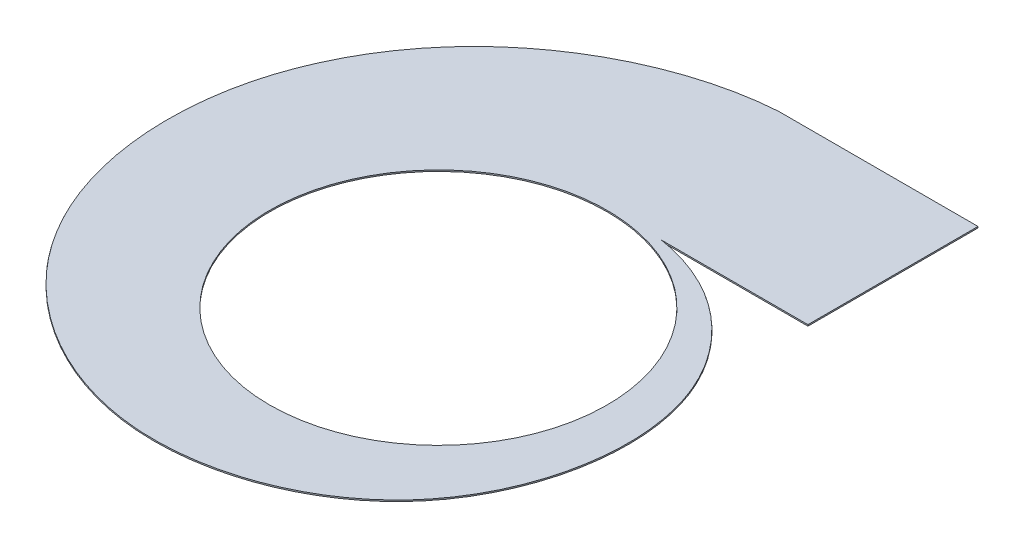
SolidWorks part; units mm, degrees
ref_plane "Front Plane" through (0, 0, 0) normal (0, 0, 1) x (1, 0, 0)
ref_plane "Top Plane" through (0, 0, 0) normal (0, 1, 0) x (1, 0, 0)
ref_plane "Right Plane" through (0, 0, 0) normal (1, 0, 0) x (0, 0, -1)
sketch "Sketch2" plane through (0, 0, 0) normal (0, 1, 0) x (1, 0, 0)
  circle A0 centre (0, 0) radius 250
  dimension "D1" = 500
curve "Helix/Spiral1"
sketch "Sketch4" plane through (0, 0, 0) normal (1, 0, 0) x (0, 0, -1)
  line L1 (250, 0) -> (248, 0)
  line L2 (250, 0) -> (250, 200)
  line L3 (250, 200) -> (248, 200)
  line L4 (248, 0) -> (248, 200)
  dimension "D1" = 250
  dimension "D2" = 2
  dimension "D3" = 200
sweep "Sweep1" add profiles "Sketch4" path "Helix/Spiral1"
sketch3d "3DSketch1"
  line L0 (0, 0, 0) -> (0, 273.3614, 0) construction
sketch "Sketch5" plane through (0, 0, 0) normal (0, -1, 0) x (1, 0, 0)
  line L0 (0, -250) -> (0, -500)
  spline S0 degree 3 poles (0, -250) (8.1812, -251.3021) (16.4905, -252.2022) (33.2838, -253.165) (41.7679, -253.2276) (58.8255, -252.4898) (67.399, -251.6894) (84.5468, -249.209) (93.1211, -247.529) (110.1794, -243.282) (118.6635, -240.7149) (135.4488, -234.6958) (143.7502, -231.2437) (160.0773, -223.4662) (168.1031, -219.1409) (183.7869, -209.6384) (191.4449, -204.4612) (206.3026, -193.2864) (213.5023, -187.2887) (227.3553, -174.5137) (234.0086, -167.7364) (246.6848, -153.4526) (252.7076, -145.946) (264.0432, -130.263) (269.3559, -122.0865) (279.1976, -105.1317) (283.7264, -96.3534) (291.933, -78.271) (295.6107, -68.9668) (302.0553, -49.9163) (304.8221, -40.1699) (309.3934, -20.325) (311.1979, -10.2265) (313.8021, 10.2265) (314.6018, 20.5811) (315.1636, 41.4454) (314.9257, 51.9551) (313.3899, 73.0247) (312.0919, 83.5846) (308.4241, 104.6469) (306.0542, 115.1492) (300.2417, 135.9868) (296.7991, 146.322) (288.8517, 166.7149) (284.3469, 176.7727) (274.2968, 196.5011) (268.7516, 206.1716) (256.654, 225.0176) (250.1016, 234.1929) (236.0343, 251.943) (228.5193, 260.5179) (212.5823, 276.9659) (204.1602, 284.8391) (186.4751, 299.7879) (177.2121, 306.8635) (157.9215, 320.1274) (147.8939, 326.3157) (127.1598, 337.7227) (116.4534, 342.9415) (94.4565, 352.3355) (83.166, 356.5108) (60.1035, 363.7534) (48.3315, 366.8207) (24.4156, 371.793) (12.2718, 373.6979) (-12.2718, 376.3021) (-24.6717, 377.0013) (-49.6069, 377.1621) (-62.1422, 376.6238) (-87.2238, 374.2899) (-99.7701, 372.4944) (-124.7469, 367.6391) (-137.1773, 364.5794) (-161.7941, 357.2015) (-173.9805, 352.8834) (-197.981, 343.0076) (-209.7952, 337.45) (-232.9248, 325.1273) (-244.2402, 318.3622) (-266.2482, 303.6696) (-276.9408, 295.742) (-297.5835, 278.7822) (-307.5335, 269.7499) (-326.5766, 250.6508) (-335.6697, 240.584) (-352.8911, 219.4976) (-361.0194, 208.4782) (-376.2116, 185.58) (-383.2754, 173.7012) (-396.2479, 149.1879) (-402.1565, 136.5535) (-412.738, 110.6421) (-417.4109, 97.3652) (-425.4515, 70.2906) (-428.8193, 56.493) (-434.1925, 28.5062) (-436.1979, 14.3172) (-438.8021, -14.3172) (-439.4008, -28.7623) (-439.1607, -57.7684) (-438.3219, -72.3293) (-435.19, -101.423) (-432.8969, -115.9557) (-426.8542, -144.8469) (-423.1046, -159.2054) (-414.1613, -187.6014) (-408.9676, -201.639) (-397.1636, -229.2471) (-390.5532, -242.8177) (-375.9579, -269.3486) (-367.9729, -282.3087) (-350.6852, -307.4788) (-341.3825, -319.6887) (-321.5301, -343.2239) (-310.9806, -354.5491) (-288.7193, -376.1873) (-277.0077, -386.5002) (-252.5202, -405.9943) (-239.7443, -415.1754) (-213.2385, -432.2959) (-199.5085, -440.2352) (-171.216, -454.7731) (-156.6535, -461.3716) (-126.8276, -473.1405) (-111.5643, -478.3109) (-80.4777, -487.1496) (-64.6545, -490.8178) (-32.5969, -496.592) (-16.3625, -498.6979) (0, -500) knots 0 0 0 0 0.015625 0.015625 0.03125 0.03125 0.046875 0.046875 0.0625 0.0625 0.078125 0.078125 0.09375 0.09375 0.109375 0.109375 0.125 0.125 0.140625 0.140625 0.15625 0.15625 0.171875 0.171875 0.1875 0.1875 0.203125 0.203125 0.21875 0.21875 0.234375 0.234375 0.25 0.25 0.265625 0.265625 0.28125 0.28125 0.296875 0.296875 0.3125 0.3125 0.328125 0.328125 0.34375 0.34375 0.359375 0.359375 0.375 0.375 0.390625 0.390625 0.40625 0.40625 0.421875 0.421875 0.4375 0.4375 0.453125 0.453125 0.46875 0.46875 0.484375 0.484375 0.5 0.5 0.515625 0.515625 0.53125 0.53125 0.546875 0.546875 0.5625 0.5625 0.578125 0.578125 0.59375 0.59375 0.609375 0.609375 0.625 0.625 0.640625 0.640625 0.65625 0.65625 0.671875 0.671875 0.6875 0.6875 0.703125 0.703125 0.71875 0.71875 0.734375 0.734375 0.75 0.75 0.765625 0.765625 0.78125 0.78125 0.796875 0.796875 0.8125 0.8125 0.828125 0.828125 0.84375 0.84375 0.859375 0.859375 0.875 0.875 0.890625 0.890625 0.90625 0.90625 0.921875 0.921875 0.9375 0.9375 0.953125 0.953125 0.96875 0.96875 0.984375 0.984375 1 1 1 1 construction
  spline S2 degree 3 poles (0, -500) (-121.7357, -491.4323) (-313.7004, -396.4417) (-452.5269, -136.2731) (-438.4955, 84.5435) (-316.9902, 288.5603) (-69.9789, 425.7522) (285.0531, 296.7827) (348.1311, -49.5077) (180.6495, -235.1223) (56.0183, -259.0814) (0, -250) knots 0 0 0 0 0.15882 0.252448 0.369226 0.425419 0.556945 0.698899 0.846399 0.926374 1 1 1 1
  point P0 (0, -500)
  point P1 (-91.7728, -483.9175)
  point P3 (-324.8629, -339.1036)
  point P6 (-425.9648, -147.4337)
  point P7 (-407.9961, 122.2472)
  point P8 (-341.1592, 233.8163)
  point P9 (-71.8416, 375.7105)
  point P10 (233.5511, 254.5527)
  point P11 (290.1309, -82.1105)
  point P12 (166.4927, -219.8621)
  point P13 (25.2431, -252.7038)
  point P14 (0, -250)
extrude "Boss-Extrude1" add sketch "Sketch5" along normal blind 2 contours S2 L0
sketch "Sketch6" plane through (0, 0, 0) normal (1, 0, 0) x (0, 0, -1)
  line L0 (-377.0896, 0) -> (-350.0924, 0) construction
  line L1 (-650.5942, 405.3229) -> (754.4117, 405.3229)
  line L2 (-650.5942, 405.3229) -> (-650.5942, 0)
  line L3 (-650.5942, 0) -> (754.4117, 0)
  line L4 (754.4117, 405.3229) -> (754.4117, 0)
extrude "Cut-Extrude1" cut sketch "Sketch6" against normal through all and the other way through all
sketch "Sketch7" plane through (0, 0, 0) normal (0, 1, 0) x (1, 0, 0)
  circle A0 centre (0, 0) radius 248
  dimension "D1" = 496
extrude "Cut-Extrude2" cut sketch "Sketch7" against normal blind 10
sketch "Sketch9" plane through (0, 0, 0) normal (0, 1, 0) x (1, 0, 0)
  line L1 (0, 500) -> (293.2591, 500)
  line L2 (0, 500) -> (0, 250)
  line L3 (0, 250) -> (293.2591, 250)
  line L4 (293.2591, 500) -> (293.2591, 250)
extrude "Boss-Extrude3" add sketch "Sketch9" against normal blind 2 contours L3 L4 L1 L2
